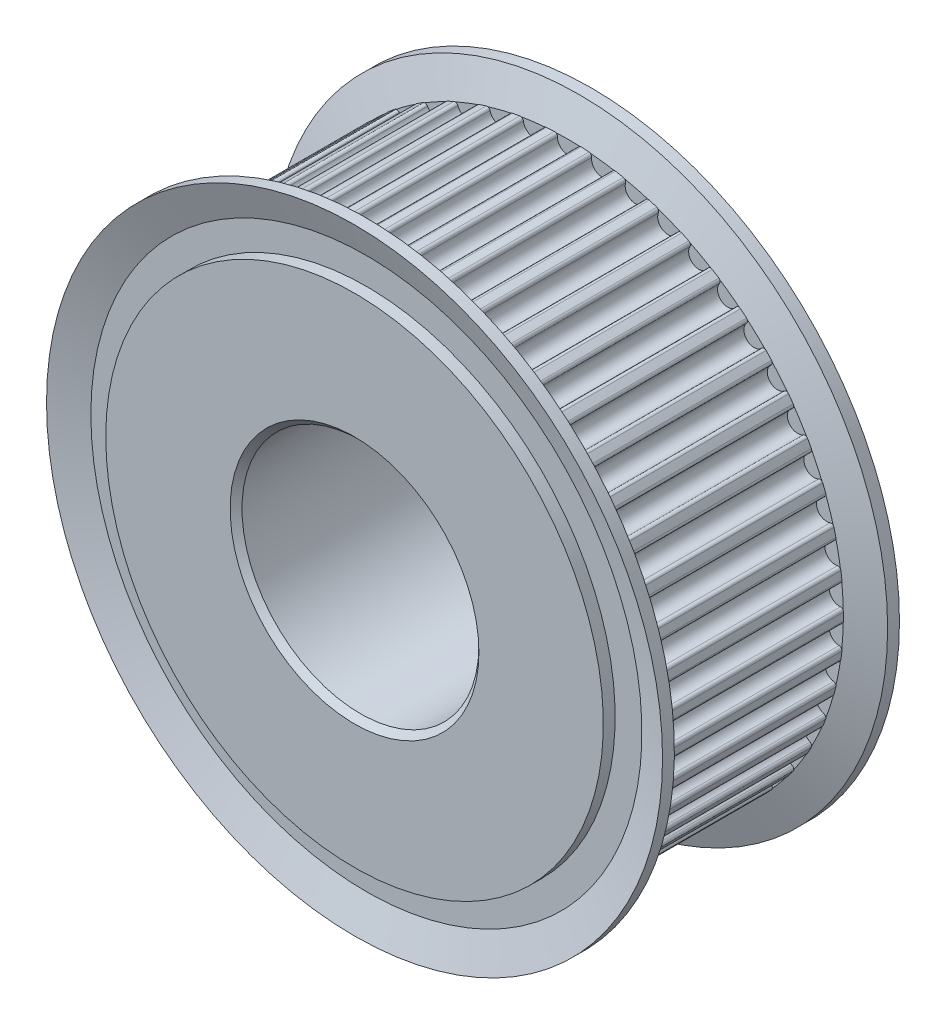
SolidWorks part; units mm, degrees
ref_plane "Front Plane" through (0, 0, 0) normal (0, 0, 1) x (1, 0, 0)
ref_plane "Top Plane" through (0, 0, 0) normal (0, 1, 0) x (1, 0, 0)
ref_plane "Right Plane" through (0, 0, 0) normal (1, 0, 0) x (0, 0, -1)
sketch "Sketch1" plane through (0, 0, 0) normal (0, 0, 1) x (1, 0, 0)
  circle A0 centre (0, 0) radius 23.875
  dimension "D1" = 47.75
extrude "Base" add sketch "Sketch1" against normal mid plane 16
sketch "Sketch2" plane through (0, 0, 0) normal (0, 0, 1) x (1, 0, 0)
  line L0 (0, 0) -> (-1.4612, 23.2391) construction
  line L1 (0, 0) -> (1.4629, 23.239) construction
  line L2 (0, 0) -> (0, 23.875) construction
  line L3 (-1.4612, 23.2391) -> (-1.4982, 23.8279)
  line L4 (1.4629, 23.239) -> (1.5, 23.8278)
  circle A0 centre (0, 0) radius 23.875 construction
  arc A1 (1.5, 23.8278) -> (-1.4982, 23.8279) centre (0, 0) ccw
  arc A2 (-1.1319, 23.2575) -> (-1.4612, 23.2391) centre (0, 0) ccw
  arc A3 (-0.8698, 23.0027) -> (0.8698, 23.0027) centre (0, 22.985) ccw
  arc A4 (-0.8698, 23.0027) -> (-1.1319, 23.2575) centre (-1.1198, 23.0078) ccw
  arc A5 (1.1319, 23.2575) -> (0.8698, 23.0027) centre (1.1198, 23.0078) ccw
  arc A6 (1.4629, 23.239) -> (1.1319, 23.2575) centre (0, 0) ccw
  dimension "D3" = 46.57
  dimension "D4" = 1.74
  dimension "D5" = 0.5
  dimension "D1" = 7.2
  dimension "D2" = 1.5
  dimension "D6" = 0.89
extrude "ToothCut" cut sketch "Sketch2" against normal through all both and the other way through all
pattern_circular "TeethCuts" count 50 over 360 about axis through (0, 0, 0) along (0, 0, 1) of "ToothCut"
sketch "Sketch6" plane through (0, 0, 0) normal (1, 0, 0) x (0, 0, -1)
  line L0 (-8, 23.2575) -> (-9, 26)
  line L1 (-9, 26) -> (-10, 26)
  line L2 (-10, 26) -> (-9, 23.2575)
  line L3 (-9, 23.2575) -> (-9, 21)
  line L4 (-9, 21) -> (-10, 21)
  line L5 (-10, 21) -> (-10, 0)
  line L6 (-10, 0) -> (-8, 0)
  line L7 (-8, 0.3307) -> (-8, -0.3307) construction
  line L8 (-8, 0) -> (-8, 23.2575)
  line L9 (0, 23.2575) -> (0, -23.2575) construction
  line L10 (8, 23.2575) -> (-8, 23.2575) construction
  line L11 (8, -23.2575) -> (-8, -23.2575) construction
  line L12 (8, 0) -> (8, 23.2575)
  line L13 (10, 0) -> (8, 0)
  line L14 (10, 21) -> (10, 0)
  line L15 (9, 21) -> (10, 21)
  line L16 (9, 23.2575) -> (9, 21)
  line L17 (10, 26) -> (9, 23.2575)
  line L18 (9, 26) -> (10, 26)
  line L19 (8, 23.2575) -> (9, 26)
  point P25 (8.5, 24.6287)
  point P26 (-8.5, 24.6287)
  dimension "D1" = 17
  dimension "D2" = 20
  dimension "D3" = 26
  dimension "D4" = 21
revolve "Flange" add sketch "Sketch6" angle 360 about axis through (0, 0, -8) along (0, 0, 1)
sketch "Sketch7" plane through (0, 0, 0) normal (0, 0, 1) x (1, 0, 0)
  line L0 (-2.485, 9.0441) -> (2.485, 9.0441)
  line L1 (2.485, 9.0441) -> (2.485, 6.5441)
  line L2 (-2.485, 9.0441) -> (-2.485, 6.5441)
  arc A0 (-2.485, 6.5441) -> (2.485, 6.5441) centre (0, 0) ccw
  point P8 (0, 9.0441)
  dimension "D2" = 14
  dimension "D1" = 4.97
  dimension "D3" = 2.5
extrude "Bore and Keyway" cut sketch "Sketch7" against normal through all both and the other way through all
chamfer "BoreChamfer" distance 0.25 angle 45 8 edges at (0, -7, 10) (2.485, 7.7941, -10) (0, 9.0441, -10) (-2.485, 7.7941, -10) (0, -7, -10) (-2.485, 7.7941, 10) (0, 9.0441, 10) (2.485, 7.7941, 10)
sketch "Sketch8" plane through (0, 0, 10) normal (0, 0, 1) x (1, 0, 0)
  circle A1 centre (0, 0) radius 10
  dimension "D1" = 20
extrude "Cut-Extrude1" cut sketch "Sketch8" against normal through all
chamfer "Chamfer1" distance 0.5 angle 45 2 edges at (10, 0, 10) (10, 0, -10)
equation "\"N\"= 50'Number of teeth"
equation "\"P\"= 3'Pitch length"
equation "\"DP\"= ( \"N\" * \"P\" ) / ( PI )'Pitch circle diameter"
equation "\"R\"= 0.87"
equation "\"R2\"= 0.25"
equation "\"B\"= 2.40"
equation "\"T\"= 1.22"
equation "\"Tooth angle\"= ( 360 / \"N\" )"
